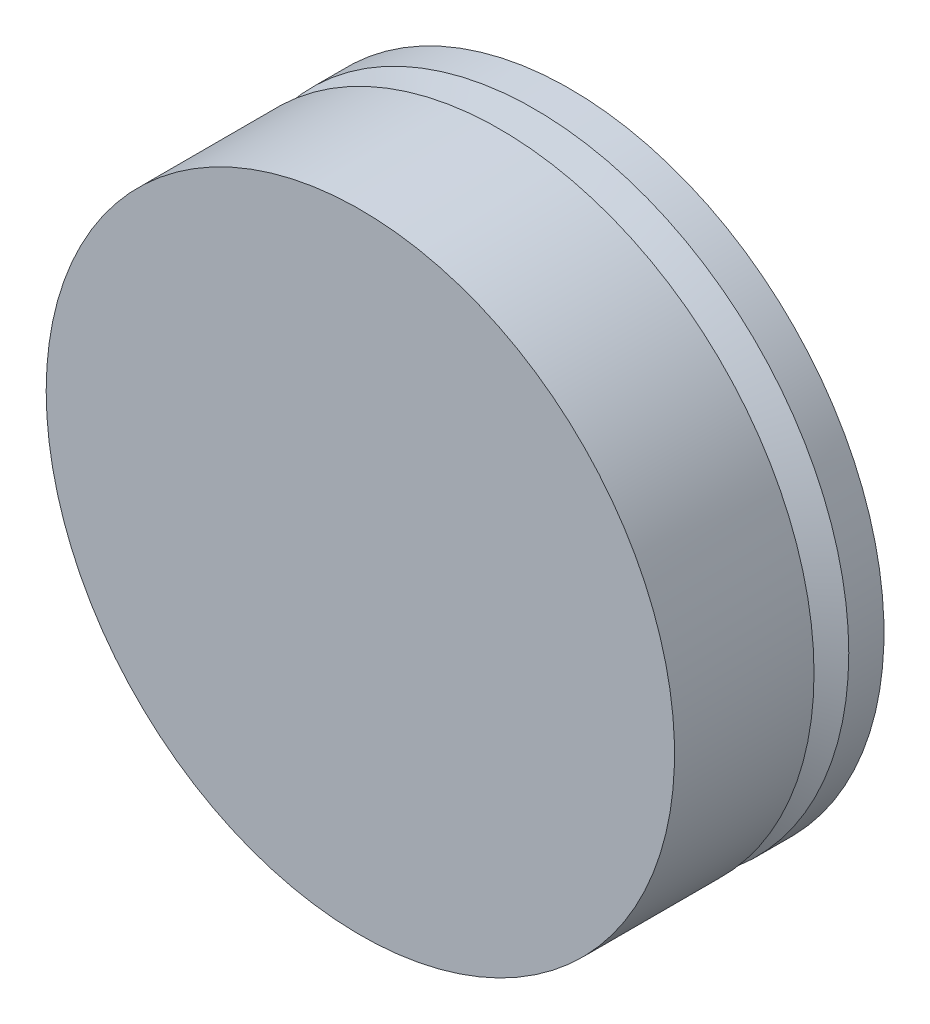
SolidWorks part; units mm, degrees
material "Plain Carbon Steel"
ref_plane "Front Plane" through (0, 0, 0) normal (0, 0, 1) x (1, 0, 0)
ref_plane "Top Plane" through (0, 0, 0) normal (0, 1, 0) x (1, 0, 0)
ref_plane "Right Plane" through (0, 0, 0) normal (1, 0, 0) x (0, 0, -1)
sketch "Sketch1" plane through (0, 0, 0) normal (0, 1, 0) x (1, 0, 0)
  line L2 (-6, 2) -> (6, 2)
  line L3 (-6, 2) -> (-6, -2)
  line L4 (-6, -2) -> (6, -2)
  line L5 (6, 2) -> (6, -2)
  line L6 (-6, 2) -> (6, -2) construction
  line L7 (-6, -2) -> (6, 2) construction
  point P0 (0, 0)
  point P1 (0, 0)
  point P5 (0, 0)
  dimension "D2" = 12
  dimension "D3" = 4
extrude "Boss-Extrude1" add sketch "Sketch1" along normal blind 12
sketch "Sketch2" plane through (0, 0, -2) normal (0, 0, -1) x (-1, 0, 0)
  line L0 (0, 0) -> (0, 12) construction
  line L1 (-6, 0) -> (6, 0) construction
  line L2 (-6, 12) -> (6, 12) construction
  circle A0 centre (0, 6) radius 6
  dimension "D1" = 12
extrude "Cut-Extrude1" cut sketch "Sketch2" against normal blind 12 flip side to cut
sketch "Sketch3" plane through (0, 0, -2) normal (0, 0, -1) x (-1, 0, 0)
  circle A0 centre (0, 6) radius 3.2
  dimension "D1" = 6.4
extrude "Cut-Extrude2" [suppressed] cut sketch "Sketch3" against normal blind 12
sketch "Sketch4" [suppressed] plane through (0, 0, 2) normal (0, 0, 1) x (1, 0, 0)
  circle A0 centre (0, 6) radius 3.55
  dimension "D1" = 7.1
extrude "Cut-Extrude3" [suppressed] cut sketch "Sketch4" against normal blind 2
sketch "Sketch5" plane through (0, 0, 0) normal (1, 0, 0) x (0, 0, -1)
  line L5 (0.6637, 10.775) -> (1.3273, 12)
  line L7 (1.3273, 12) -> (0.6637, 12)
  line L8 (0.6637, 12) -> (0.6637, 10.775)
ref_point "Point1" [suppressed]
ref_axis "Axis1" [suppressed] through (0, 6, 0) along (0, 0, -1)
revolve "Cut-Revolve1" cut sketch "Sketch5" angle 360 about axis through (0, 6, 0) along (0, 0, -1)
